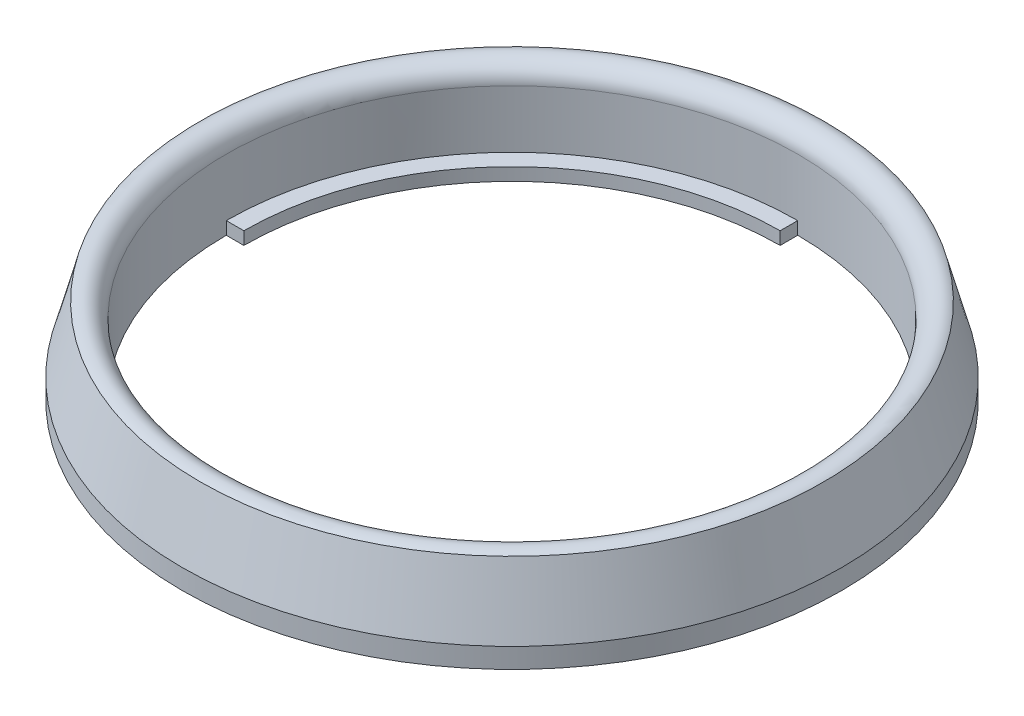
SolidWorks part; units mm, degrees
ref_plane "Front Plane" through (0, 0, 0) normal (0, 0, 1) x (1, 0, 0)
ref_plane "Top Plane" through (0, 0, 0) normal (0, 1, 0) x (1, 0, 0)
ref_plane "Right Plane" through (0, 0, 0) normal (1, 0, 0) x (0, 0, -1)
sketch "Sketch1" plane through (0, 0, 0) normal (0, 0, 1) x (1, 0, 0)
  line L0 (37.5, 0) -> (30.5, 0)
  line L1 (30.5, 0) -> (30.5, 1.45)
  line L2 (30.5, 1.45) -> (32.5, 1.45)
  line L3 (32.5, 1.45) -> (32.5, 8)
  line L4 (37.5, 0) -> (37.5, 2.2679)
  line L5 (37.5, 2.2679) -> (35.5, 9.7321)
  line L6 (34.5, 8) -> (32.5, 8) construction
  line L7 (34.5, 8) -> (35.5, 9.7321) construction
  line L8 (35.5, 9.7321) -> (35.5, 0) construction
  line L9 (34.5, 8) -> (34.5, 10) construction
  line L10 (32.5, 1.45) -> (32.5, 0) construction
  line L11 (32.5, 0) -> (0, 0) construction
  line L12 (0, 0) -> (0, 8.4748) construction
  arc A0 (32.5, 8) -> (35.5, 9.7321) centre (34.5, 8) cw
revolve "Revolve1" add sketch "Sketch1" angle 360 about L12
sketch "Sketch2" plane through (0, 0, 0) normal (0, 1, 0) x (1, 0, 0)
  line L0 (0, -32.5) -> (0, 32.5) construction
  line L1 (32.5, 0) -> (-32.5, 0) construction
  line L2 (0, 30.5) -> (0, 32.5)
  line L3 (32.5, 0) -> (30.5, 0)
  line L4 (0, -32.5) -> (0, -30.5)
  line L5 (-30.5, 0) -> (-32.5, 0)
  arc A0 (-30.5, 0) -> (0, -30.5) centre (0, 0) ccw
  arc A1 (-32.5, 0) -> (0, -32.5) centre (0, 0) ccw
  arc A5 (30.5, 0) -> (0, 30.5) centre (0, 0) ccw
  arc A6 (32.5, 0) -> (0, 32.5) centre (0, 0) ccw
  circle A7 centre (0, 0) radius 30.5 construction
  circle A8 centre (0, 0) radius 32.5 construction
extrude "Cut-Extrude2" cut sketch "Sketch2" along normal through all
equation "\"Lens_D1\"= 61mm'lens inner diameter"
equation "\"Slot_H\"= 1.45mm'height of connecting slot between lens and 3d printed parted"
equation "\"3D_H1\"= 10mm'height of 1st 3D printed piece"
equation "\"Slot_T\"= 2mm'thickness of connecting slot"
equation "\"3D_T1\"= 5mm'thickness of first 3D printed lense piece"
equation "\"F_T\"= 1mm'film thickness"
equation "\"3D_A1\"= 120deg'angle of contact for first 3d piece"
equation "\"3D_A2\"= 15deg'slope of side for first 3D printed piece"
equation "\"D1@Sketch1\"=\"Slot_T\""
equation "\"D2@Sketch1\"=\"Slot_H\""
equation "\"D4@Sketch1\"=\"3D_A1\""
equation "\"D5@Sketch1\"=\"3D_A2\""
equation "\"D6@Sketch1\"=\"3D_H1\""
equation "\"3D_R1\"= 2mm'top radius for 1st 3d printed piece"
equation "\"D8@Sketch1\"=\"3D_R1\""
equation "\"D7@Sketch1\"=\"Lens_D1\"/2"
